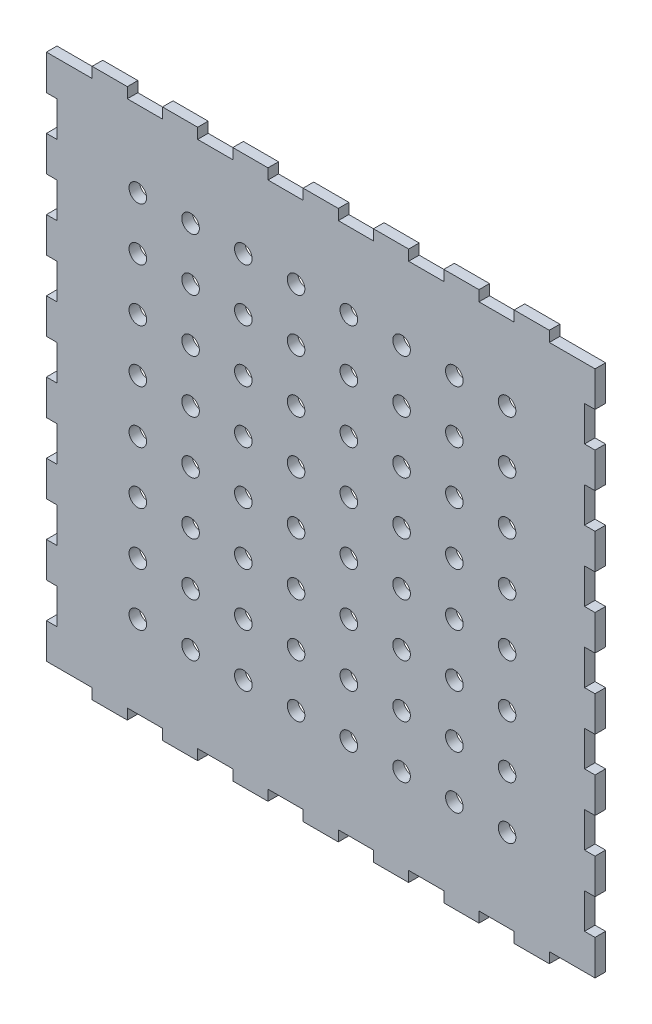
SolidWorks part; units mm, degrees
ref_plane "Front Plane" through (0, 0, 0) normal (0, 0, 1) x (1, 0, 0)
ref_plane "Top Plane" through (0, 0, 0) normal (0, 1, 0) x (1, 0, 0)
ref_plane "Right Plane" through (0, 0, 0) normal (1, 0, 0) x (0, 0, -1)
sketch "Sketch2" plane through (0, 0, 0) normal (0, 0, 1) x (1, 0, 0)
  line L0 (156.2307, -0.1184) -> (153.2307, -0.1184)
  line L1 (133.2307, -0.1184) -> (133.2307, -3.1184)
  line L2 (0.2307, -0.1184) -> (0.2307, 9.8816)
  line L3 (153.2307, -0.1184) -> (143.2307, -0.1184)
  line L4 (0.2307, 9.8816) -> (3.2307, 9.8816)
  line L5 (143.2307, -0.1184) -> (143.2307, -3.1184)
  line L6 (143.2307, -3.1184) -> (133.2307, -3.1184)
  line L7 (133.2307, -0.1184) -> (123.2307, -0.1184)
  line L8 (123.2307, -3.1184) -> (113.2307, -3.1184)
  line L9 (123.2307, -0.1184) -> (123.2307, -3.1184)
  line L10 (113.2307, -0.1184) -> (113.2307, -3.1184)
  line L11 (113.2307, -0.1184) -> (103.2307, -0.1184)
  line L12 (103.2307, -3.1184) -> (93.2307, -3.1184)
  line L13 (103.2307, -0.1184) -> (103.2307, -3.1184)
  line L14 (93.2307, -0.1184) -> (93.2307, -3.1184)
  line L15 (93.2307, -0.1184) -> (83.2307, -0.1184)
  line L16 (83.2307, -3.1184) -> (73.2307, -3.1184)
  line L17 (83.2307, -0.1184) -> (83.2307, -3.1184)
  line L18 (73.2307, -0.1184) -> (73.2307, -3.1184)
  line L19 (73.2307, -0.1184) -> (63.2307, -0.1184)
  line L20 (63.2307, -3.1184) -> (53.2307, -3.1184)
  line L21 (63.2307, -0.1184) -> (63.2307, -3.1184)
  line L22 (53.2307, -0.1184) -> (53.2307, -3.1184)
  line L23 (53.2307, -0.1184) -> (43.2307, -0.1184)
  line L24 (43.2307, -3.1184) -> (33.2307, -3.1184)
  line L25 (43.2307, -0.1184) -> (43.2307, -3.1184)
  line L26 (33.2307, -0.1184) -> (33.2307, -3.1184)
  line L27 (33.2307, -0.1184) -> (23.2307, -0.1184)
  line L28 (23.2307, -3.1184) -> (13.2307, -3.1184)
  line L29 (23.2307, -0.1184) -> (23.2307, -3.1184)
  line L30 (13.2307, -3.1184) -> (13.2307, -0.1184)
  line L31 (13.2307, -0.1184) -> (3.2307, -0.1184)
  line L32 (3.2307, -0.1184) -> (0.2307, -0.1184)
  line L33 (3.2307, 9.8816) -> (3.2307, 19.8816)
  line L34 (0.2307, 19.8816) -> (0.2307, 29.8816)
  line L35 (0.2307, 29.8816) -> (3.2307, 29.8816)
  line L36 (3.2307, 29.8816) -> (3.2307, 39.8816)
  line L37 (3.2307, 19.8816) -> (0.2307, 19.8816)
  line L38 (0.2307, 39.8816) -> (0.2307, 49.8816)
  line L39 (0.2307, 49.8816) -> (3.2307, 49.8816)
  line L40 (3.2307, 49.8816) -> (3.2307, 59.8816)
  line L41 (3.2307, 39.8816) -> (0.2307, 39.8816)
  line L42 (0.2307, 59.8816) -> (0.2307, 69.8816)
  line L43 (0.2307, 69.8816) -> (3.2307, 69.8816)
  line L44 (3.2307, 69.8816) -> (3.2307, 79.8816)
  line L45 (3.2307, 59.8816) -> (0.2307, 59.8816)
  line L46 (0.2307, 79.8816) -> (0.2307, 89.8816)
  line L47 (0.2307, 89.8816) -> (3.2307, 89.8816)
  line L48 (3.2307, 89.8816) -> (3.2307, 99.8816)
  line L49 (3.2307, 79.8816) -> (0.2307, 79.8816)
  line L50 (0.2307, 99.8816) -> (0.2307, 109.8816)
  line L51 (3.2307, 139.8816) -> (0.2307, 139.8816)
  line L52 (0.2307, 109.8816) -> (3.2307, 109.8816)
  line L53 (3.2307, 109.8816) -> (3.2307, 119.8816)
  line L54 (3.2307, 99.8816) -> (0.2307, 99.8816)
  line L55 (0.2307, 119.8816) -> (0.2307, 129.8816)
  line L56 (0.2307, 129.8816) -> (3.2307, 129.8816)
  line L57 (3.2307, 129.8816) -> (3.2307, 139.8816)
  line L58 (3.2307, 119.8816) -> (0.2307, 119.8816)
  line L59 (0.2307, 139.8816) -> (0.2307, 149.8875)
  line L60 (156.2307, 139.8816) -> (156.2307, 149.8875)
  line L61 (3.2307, 149.8875) -> (153.2307, 149.8875) construction
  line L62 (153.2307, -0.1184) -> (153.2307, 149.8875) construction
  line L63 (153.2307, 119.8816) -> (156.2307, 119.8816)
  line L64 (153.2307, 129.8816) -> (153.2307, 139.8816)
  line L65 (156.2307, 129.8816) -> (153.2307, 129.8816)
  line L66 (156.2307, 119.8816) -> (156.2307, 129.8816)
  line L67 (153.2307, 99.8816) -> (156.2307, 99.8816)
  line L68 (153.2307, 109.8816) -> (153.2307, 119.8816)
  line L69 (156.2307, 109.8816) -> (153.2307, 109.8816)
  line L70 (153.2307, 139.8816) -> (156.2307, 139.8816)
  line L71 (156.2307, 99.8816) -> (156.2307, 109.8816)
  line L72 (153.2307, 79.8816) -> (156.2307, 79.8816)
  line L73 (153.2307, 89.8816) -> (153.2307, 99.8816)
  line L74 (156.2307, 89.8816) -> (153.2307, 89.8816)
  line L75 (156.2307, 79.8816) -> (156.2307, 89.8816)
  line L76 (153.2307, 59.8816) -> (156.2307, 59.8816)
  line L77 (153.2307, 69.8816) -> (153.2307, 79.8816)
  line L78 (156.2307, 69.8816) -> (153.2307, 69.8816)
  line L79 (156.2307, 59.8816) -> (156.2307, 69.8816)
  line L80 (153.2307, 39.8816) -> (156.2307, 39.8816)
  line L81 (153.2307, 49.8816) -> (153.2307, 59.8816)
  line L82 (156.2307, 49.8816) -> (153.2307, 49.8816)
  line L83 (156.2307, 39.8816) -> (156.2307, 49.8816)
  line L84 (153.2307, 19.8816) -> (156.2307, 19.8816)
  line L85 (153.2307, 29.8816) -> (153.2307, 39.8816)
  line L86 (156.2307, 29.8816) -> (153.2307, 29.8816)
  line L87 (156.2307, 19.8816) -> (156.2307, 29.8816)
  line L88 (153.2307, 9.8816) -> (153.2307, 19.8816)
  line L89 (153.2307, -0.1184) -> (156.2307, -0.1184)
  line L90 (156.2307, 9.8816) -> (153.2307, 9.8816)
  line L91 (156.2307, -0.1184) -> (156.2307, 9.8816)
  line L92 (153.2307, -0.1184) -> (3.2307, -0.1184) construction
  line L93 (3.2307, 149.8875) -> (3.2307, -0.1184) construction
  line L96 (153.2307, 149.8875) -> (156.2307, 149.8875)
  line L97 (3.2307, 149.8875) -> (0.2307, 149.8875)
  line L98 (13.2307, 149.8875) -> (3.2307, 149.8875)
  line L99 (13.2307, 152.8875) -> (13.2307, 149.8875)
  line L100 (23.2307, 149.8875) -> (23.2307, 152.8875)
  line L101 (23.2307, 152.8875) -> (13.2307, 152.8875)
  line L102 (33.2307, 149.8875) -> (23.2307, 149.8875)
  line L103 (33.2307, 149.8875) -> (33.2307, 152.8875)
  line L104 (43.2307, 149.8875) -> (43.2307, 152.8875)
  line L105 (43.2307, 152.8875) -> (33.2307, 152.8875)
  line L106 (53.2307, 149.8875) -> (43.2307, 149.8875)
  line L107 (53.2307, 149.8875) -> (53.2307, 152.8875)
  line L108 (63.2307, 149.8875) -> (63.2307, 152.8875)
  line L109 (63.2307, 152.8875) -> (53.2307, 152.8875)
  line L110 (73.2307, 149.8875) -> (63.2307, 149.8875)
  line L111 (73.2307, 149.8875) -> (73.2307, 152.8875)
  line L112 (83.2307, 149.8875) -> (83.2307, 152.8875)
  line L113 (83.2307, 152.8875) -> (73.2307, 152.8875)
  line L114 (93.2307, 149.8875) -> (83.2307, 149.8875)
  line L115 (93.2307, 149.8875) -> (93.2307, 152.8875)
  line L116 (103.2307, 149.8875) -> (103.2307, 152.8875)
  line L117 (103.2307, 152.8875) -> (93.2307, 152.8875)
  line L118 (113.2307, 149.8875) -> (103.2307, 149.8875)
  line L119 (113.2307, 149.8875) -> (113.2307, 152.8875)
  line L120 (123.2307, 149.8875) -> (123.2307, 152.8875)
  line L121 (123.2307, 152.8875) -> (113.2307, 152.8875)
  line L122 (133.2307, 149.8875) -> (123.2307, 149.8875)
  line L123 (143.2307, 152.8875) -> (133.2307, 152.8875)
  line L124 (143.2307, 149.8875) -> (143.2307, 152.8875)
  line L125 (153.2307, 149.8875) -> (143.2307, 149.8875)
  line L126 (133.2307, 149.8875) -> (133.2307, 152.8875)
  line L127 (156.2307, 149.8875) -> (153.2307, 149.8875)
  line L131 (16.1531, 12.8045) -> (140.3083, 12.8045)
  circle A0 centre (26.2194, 128.2261) radius 2.5
  circle A1 centre (41.2194, 128.2261) radius 2.5
  circle A2 centre (56.2194, 128.2261) radius 2.5
  circle A3 centre (71.2194, 128.2261) radius 2.5
  circle A4 centre (86.2194, 128.2261) radius 2.5
  circle A5 centre (101.2194, 128.2261) radius 2.5
  circle A6 centre (116.2194, 128.2261) radius 2.5
  circle A7 centre (131.2194, 128.2261) radius 2.5
  circle A8 centre (26.2194, 113.2261) radius 2.5
  circle A9 centre (41.2194, 113.2261) radius 2.5
  circle A10 centre (56.2194, 113.2261) radius 2.5
  circle A11 centre (71.2194, 113.2261) radius 2.5
  circle A12 centre (86.2194, 113.2261) radius 2.5
  circle A13 centre (101.2194, 113.2261) radius 2.5
  circle A14 centre (116.2194, 113.2261) radius 2.5
  circle A15 centre (131.2194, 113.2261) radius 2.5
  circle A16 centre (26.2194, 98.2261) radius 2.5
  circle A17 centre (41.2194, 98.2261) radius 2.5
  circle A18 centre (56.2194, 98.2261) radius 2.5
  circle A19 centre (71.2194, 98.2261) radius 2.5
  circle A20 centre (86.2194, 98.2261) radius 2.5
  circle A21 centre (101.2194, 98.2261) radius 2.5
  circle A22 centre (116.2194, 98.2261) radius 2.5
  circle A23 centre (131.2194, 98.2261) radius 2.5
  circle A24 centre (26.2194, 83.2261) radius 2.5
  circle A25 centre (41.2194, 83.2261) radius 2.5
  circle A26 centre (56.2194, 83.2261) radius 2.5
  circle A27 centre (71.2194, 83.2261) radius 2.5
  circle A28 centre (86.2194, 83.2261) radius 2.5
  circle A29 centre (101.2194, 83.2261) radius 2.5
  circle A30 centre (116.2194, 83.2261) radius 2.5
  circle A31 centre (131.2194, 83.2261) radius 2.5
  circle A32 centre (26.2194, 68.2261) radius 2.5
  circle A33 centre (41.2194, 68.2261) radius 2.5
  circle A34 centre (56.2194, 68.2261) radius 2.5
  circle A35 centre (71.2194, 68.2261) radius 2.5
  circle A36 centre (86.2194, 68.2261) radius 2.5
  circle A37 centre (101.2194, 68.2261) radius 2.5
  circle A38 centre (116.2194, 68.2261) radius 2.5
  circle A39 centre (131.2194, 68.2261) radius 2.5
  circle A40 centre (26.2194, 53.2261) radius 2.5
  circle A41 centre (41.2194, 53.2261) radius 2.5
  circle A42 centre (56.2194, 53.2261) radius 2.5
  circle A43 centre (71.2194, 53.2261) radius 2.5
  circle A44 centre (86.2194, 53.2261) radius 2.5
  circle A45 centre (101.2194, 53.2261) radius 2.5
  circle A46 centre (116.2194, 53.2261) radius 2.5
  circle A47 centre (131.2194, 53.2261) radius 2.5
  circle A48 centre (26.2194, 38.2261) radius 2.5
  circle A49 centre (41.2194, 38.2261) radius 2.5
  circle A50 centre (56.2194, 38.2261) radius 2.5
  circle A51 centre (71.2194, 38.2261) radius 2.5
  circle A52 centre (86.2194, 38.2261) radius 2.5
  circle A53 centre (101.2194, 38.2261) radius 2.5
  circle A54 centre (116.2194, 38.2261) radius 2.5
  circle A55 centre (131.2194, 38.2261) radius 2.5
  circle A56 centre (26.2194, 23.2261) radius 2.5
  circle A57 centre (41.2194, 23.2261) radius 2.5
  circle A58 centre (56.2194, 23.2261) radius 2.5
  circle A59 centre (71.2194, 23.2261) radius 2.5
  circle A60 centre (86.2194, 23.2261) radius 2.5
  circle A61 centre (101.2194, 23.2261) radius 2.5
  circle A62 centre (116.2194, 23.2261) radius 2.5
  circle A63 centre (131.2194, 23.2261) radius 2.5
  point P61 (88.297, 66.1461)
  dimension "D2" = 8
  dimension "D4" = 15
  dimension "D5" = 15
  dimension "D1" = 7
  dimension "D3" = 8
extrude "Boss-Extrude2" add sketch "Sketch2" along normal blind 3 contours L126 L122 L120 L121 L119 L118 L116 L117 L115 L114 L112 L113 L111 L110 L108 L109 L107 L106 L104 L105 L103 L102 L100 L101 L99 L98 L97 L59 L51 L57 L56 L55 L58 L53 L52 L50 L54 L48 L47 L46 L49 L44 L43 L42 L45 L40 L39 L38 L41 L36 L35
